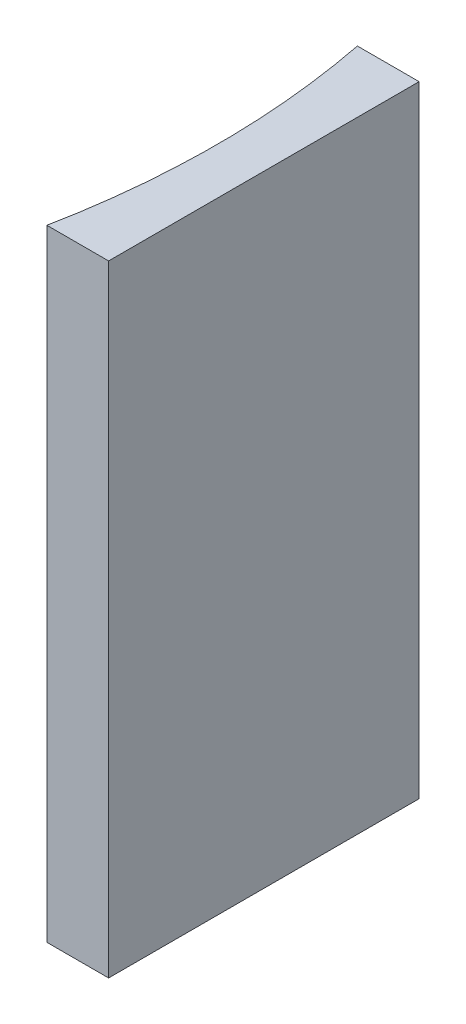
SolidWorks part; units mm, degrees
ref_plane "前视基准面" through (0, 0, 0) normal (0, 0, 1) x (1, 0, 0)
ref_plane "上视基准面" through (0, 0, 0) normal (0, 1, 0) x (1, 0, 0)
ref_plane "右视基准面" through (0, 0, 0) normal (1, 0, 0) x (0, 0, -1)
sketch "草图1" plane through (0, 0, 0) normal (0, 1, 0) x (1, 0, 0)
  line L0 (0, 0) -> (0, -20)
  line L1 (0, 0) -> (-3.9767, 0)
  line L2 (0, -20) -> (-3.9767, -20)
  line L3 (8.2336, -10) -> (-10.4405, -10) construction
  arc A0 (-3.9767, -20) -> (-3.9767, 0) centre (-54.68, -10) ccw
  point P7 (-3, -10)
  point P8 (0, -10)
  dimension "D2" = 51.68
  dimension "D3" = 3
  dimension "D1" = 20
extrude "凸台-拉伸1" add sketch "草图1" along normal blind 40
